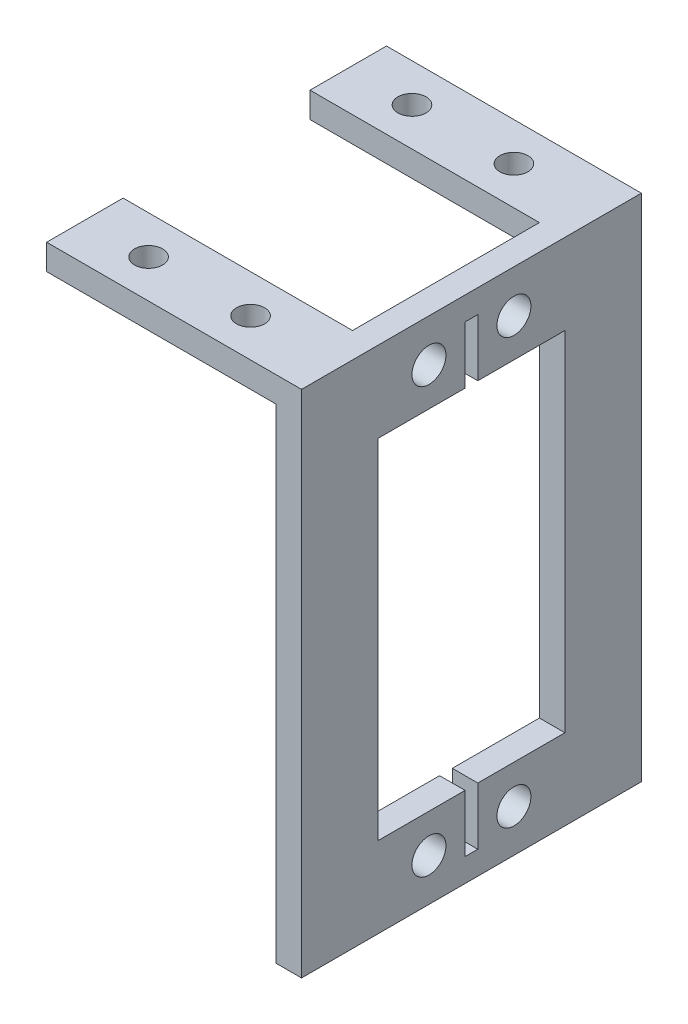
SolidWorks part; units mm, degrees
ref_plane "前视基准面" through (0, 0, 0) normal (0, 0, 1) x (1, 0, 0)
ref_plane "上视基准面" through (0, 0, 0) normal (0, 1, 0) x (1, 0, 0)
ref_plane "右视基准面" through (0, 0, 0) normal (1, 0, 0) x (0, 0, -1)
sketch "草图1" plane through (0, 0, 0) normal (0, 0, 1) x (1, 0, 0)
  line L0 (0, 0) -> (30, 0)
  line L1 (30, 0) -> (30, -60)
  line L2 (0, -3) -> (27, -3)
  line L3 (27, -3) -> (27, -60)
  line L4 (27, -60) -> (30, -60)
  line L5 (0, 0) -> (0, -3)
  dimension "D1" = 30
  dimension "D3" = 60
  dimension "D2" = 3
extrude "凸台-拉伸1" add sketch "草图1" along normal blind 40
sketch "草图2" plane through (0, 0, 0) normal (0, 1, 0) x (1, 0, 0)
  line L0 (0, 0) -> (0, -9) construction
  line L1 (0, -40) -> (0, 0) construction
  line L2 (0, -9) -> (27, -9)
  line L3 (30, -40) -> (30, 0) construction
  line L4 (27, -9) -> (27, 0) construction
  line L5 (27, 0) -> (0, 0) construction
  line L6 (0, -20) -> (30, -20) construction
  line L7 (27, -31) -> (27, -40) construction
  line L8 (0, -31) -> (27, -31)
  line L9 (0, -40) -> (0, -31) construction
  line L10 (27, -40) -> (0, -40) construction
  line L11 (27, -40) -> (27, 0) construction
  line L12 (27, -9) -> (27, -31)
  line L13 (0, -9) -> (0, -31)
  line L14 (7.5, -4.5) -> (19.5, -4.5) construction
  line L15 (13.5, -4.5) -> (13.5, 0) construction
  line L16 (13.5, -4.5) -> (13.5, -9) construction
  line L17 (30, -40) -> (30, 0) construction
  circle A0 centre (7.5, -4.5) radius 1.65
  circle A1 centre (19.5, -4.5) radius 1.65
  circle A2 centre (19.5, -35.5) radius 1.65
  circle A3 centre (7.5, -35.5) radius 1.65
  dimension "D2" = 3.3
  dimension "D3" = 12
  dimension "D1" = 9
extrude "切除-拉伸2" cut sketch "草图2" against normal blind 10
sketch "草图3" plane through (30, 0, 0) normal (1, 0, 0) x (0, 0, -1)
  line L0 (-20, 0) -> (-20, -71.9676) construction
  line L1 (-40, 0) -> (0, 0) construction
  line L2 (-25, -5) -> (-15, -5) construction
  line L3 (-40, -3) -> (-31, -3) construction
  line L4 (-15, -5) -> (-15, -55) construction
  line L5 (-15, -30) -> (-20, -30) construction
  line L6 (-20.75, -9.5) -> (-20.75, -2.75)
  line L7 (-31, -50.5) -> (-20.75, -50.5)
  line L8 (-31, -50.5) -> (-31, -9.5)
  line L9 (-31, -9.5) -> (-20.75, -9.5)
  line L10 (-9, -50.5) -> (-9, -9.5)
  line L11 (-31, -50.5) -> (-9, -9.5) construction
  line L12 (-31, -9.5) -> (-9, -50.5) construction
  line L13 (-20.75, -2.75) -> (-19.25, -2.75)
  line L14 (-19.25, -2.75) -> (-19.25, -9.5)
  line L15 (-20.75, -57.25) -> (-19.25, -57.25)
  line L16 (-20.75, -50.5) -> (-20.75, -57.25)
  line L17 (-19.25, -57.25) -> (-19.25, -50.5)
  line L18 (-19.25, -50.5) -> (-9, -50.5)
  line L19 (-19.25, -9.5) -> (-9, -9.5)
  circle A0 centre (-25, -5) radius 2
  circle A1 centre (-15, -5) radius 2
  circle A2 centre (-15, -55) radius 2
  circle A3 centre (-25, -55) radius 2
  dimension "D3" = 4
  dimension "D4" = 50
  dimension "D1" = 10
  dimension "D2" = 2
  dimension "D5" = 22
  dimension "D6" = 41
  dimension "D7" = 1.5
  dimension "D8" = 6.75
extrude "切除-拉伸3" cut sketch "草图3" against normal blind 10
